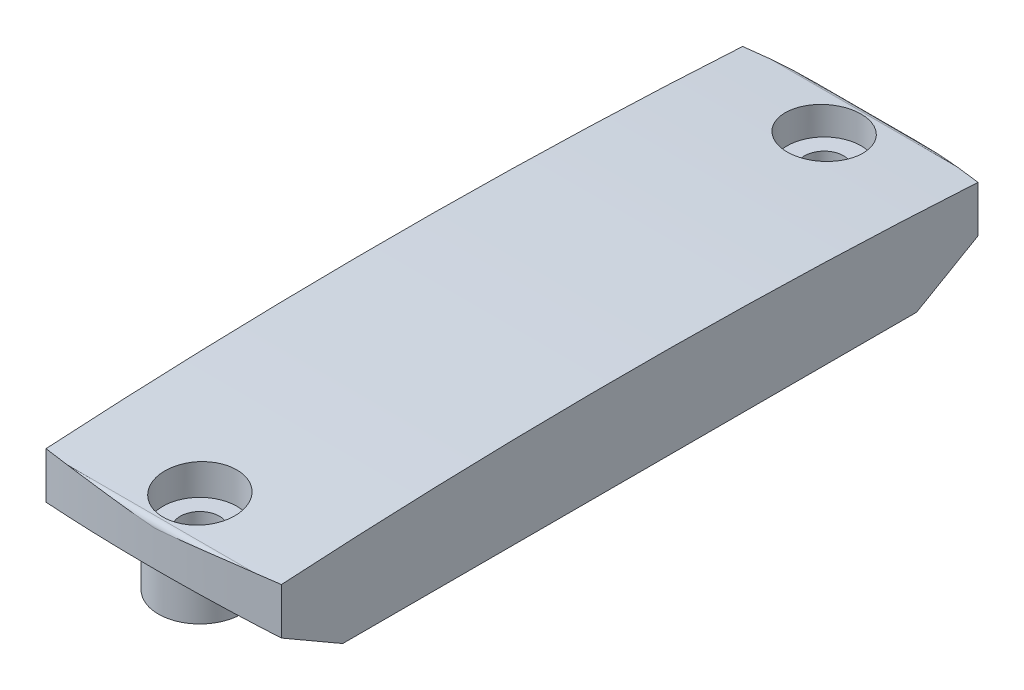
SolidWorks part; units mm, degrees
ref_plane "Front Plane" through (0, 0, 0) normal (0, 0, 1) x (1, 0, 0)
ref_plane "Top Plane" through (0, 0, 0) normal (0, 1, 0) x (1, 0, 0)
ref_plane "Right Plane" through (0, 0, 0) normal (1, 0, 0) x (0, 0, -1)
ref_plane "Plane1" through (0, 0, 0) normal (0, 1, 0) x (1, 0, 0)
sketch "Sketch1" plane through (0, 0, 0) normal (0, 1, 0) x (1, 0, 0)
  line L0 (10.2, -57.235) -> (10.2, 3.135)
  line L1 (-10.2, 3.135) -> (-10.2, -57.235)
  arc A0 (-10.2, -57.235) -> (10.2, -57.235) centre (0, 12.22) ccw
  arc A1 (10.2, 3.135) -> (-10.2, 3.135) centre (0, -66.32) ccw
extrude "Boss-Extrude1" add sketch "Sketch1" along normal blind 10
ref_plane "Plane2" through (0, 0, 0) normal (1, 0, 0) x (0, 0, -1)
sketch "Sketch2" plane through (0, 0, 0) normal (1, 0, 0) x (0, 0, -1)
  line L0 (-68.5332, -20.006) -> (15.0359, -20.006)
  line L1 (15.0359, -20.006) -> (15.0359, 28.006)
  line L2 (15.0359, 28.006) -> (-68.5332, 28.006)
  line L3 (-68.5332, 28.006) -> (-68.5332, -20.006)
  line L4 (-57.98, 6.5722) -> (-57.98, 3.5)
  line L5 (-57.98, 3.5) -> (-51.9178, 0)
  line L6 (-51.9178, 0) -> (-2.1822, 0)
  line L7 (-2.1822, 0) -> (3.88, 3.5)
  line L8 (3.88, 3.5) -> (3.88, 6.5722)
  arc A0 (3.88, 6.5722) -> (3.4105, 7.0713) centre (3.38, 6.5722) ccw
  arc A1 (3.4105, 7.0713) -> (-57.5105, 7.0713) centre (-27.05, -492) ccw
  arc A2 (-57.5105, 7.0713) -> (-57.98, 6.5722) centre (-57.48, 6.5722) ccw
extrude "Cut-Extrude1" cut sketch "Sketch2" against normal blind 12 and the other way blind 12
ref_plane "Plane3" through (0, 0, 0) normal (0, 1, 0) x (1, 0, 0)
sketch "Sketch3" plane through (0, 0, 0) normal (0, 1, 0) x (1, 0, 0)
  line L0 (-3.6, 0) -> (-3.6, -3.6)
  line L1 (-3.6, -3.6) -> (3.6, -3.6)
  line L2 (3.6, -3.6) -> (3.6, 0)
  arc A0 (3.6, 0) -> (-3.6, 0) centre (0, 0) ccw
extrude "Boss-Extrude2" add sketch "Sketch3" along normal blind 5
ref_plane "Plane4" through (0, 0, 0) normal (0, 1, 0) x (1, 0, 0)
sketch "Sketch4" plane through (0, 0, 0) normal (0, 1, 0) x (1, 0, 0)
  line L0 (3.6, -54.1) -> (3.6, -50.5)
  line L1 (3.6, -50.5) -> (-3.6, -50.5)
  line L2 (-3.6, -50.5) -> (-3.6, -54.1)
  arc A0 (-3.6, -54.1) -> (3.6, -54.1) centre (0, -54.1) ccw
extrude "Boss-Extrude3" add sketch "Sketch4" along normal blind 5
ref_plane "Plane5" through (0, 0, 0) normal (0, 1, 0) x (1, 0, 0)
sketch "Sketch5" plane through (0, 0, 0) normal (0, 1, 0) x (1, 0, 0)
  line L0 (-7.9, -50.55) -> (7.9, -50.55)
  line L1 (7.9, -50.55) -> (7.9, -3.55)
  line L2 (7.9, -3.55) -> (-7.9, -3.55)
  line L3 (-7.9, -3.55) -> (-7.9, -50.55)
extrude "Cut-Extrude2" cut sketch "Sketch5" along normal blind 6.5
ref_plane "Plane6" through (0, 0, 0) normal (1, 0, 0) x (0, 0, -1)
sketch "Sketch6" plane through (0, 0, 0) normal (1, 0, 0) x (0, 0, -1)
  line L0 (0, 0) -> (-1.5, 0)
  line L1 (-1.5, 0) -> (-1.5, 2.4)
  line L2 (-1.5, 2.4) -> (-1.35, 2.4)
  line L3 (-1.35, 2.4) -> (-1.35, 3)
  line L4 (-1.35, 3) -> (-1.7, 3.2021)
  line L5 (-1.7, 3.2021) -> (-1.7, 4.7)
  line L6 (-1.7, 4.7) -> (-3.2, 4.7)
  line L7 (-3.2, 4.7) -> (-3.2, 8)
  line L8 (-3.2, 8) -> (0, 8)
  line L9 (0, 8) -> (0, 0)
  line L10 (0, 8) -> (0, 0) construction
revolve "Cut-Revolve1" cut sketch "Sketch6" angle 360 about L10
ref_plane "Plane7" through (0, 0, 0) normal (1, 0, 0) x (0, 0, -1)
sketch "Sketch7" plane through (0, 0, 0) normal (1, 0, 0) x (0, 0, -1)
  line L0 (-54.1, 0) -> (-55.6, 0)
  line L1 (-55.6, 0) -> (-55.6, 2.4)
  line L2 (-55.6, 2.4) -> (-55.45, 2.4)
  line L3 (-55.45, 2.4) -> (-55.45, 3)
  line L4 (-55.45, 3) -> (-55.8, 3.2021)
  line L5 (-55.8, 3.2021) -> (-55.8, 4.7)
  line L6 (-55.8, 4.7) -> (-57.3, 4.7)
  line L7 (-57.3, 4.7) -> (-57.3, 8)
  line L8 (-57.3, 8) -> (-54.1, 8)
  line L9 (-54.1, 8) -> (-54.1, 0)
  line L10 (-54.1, 8) -> (-54.1, 0) construction
revolve "Cut-Revolve2" cut sketch "Sketch7" angle 360 about L10
